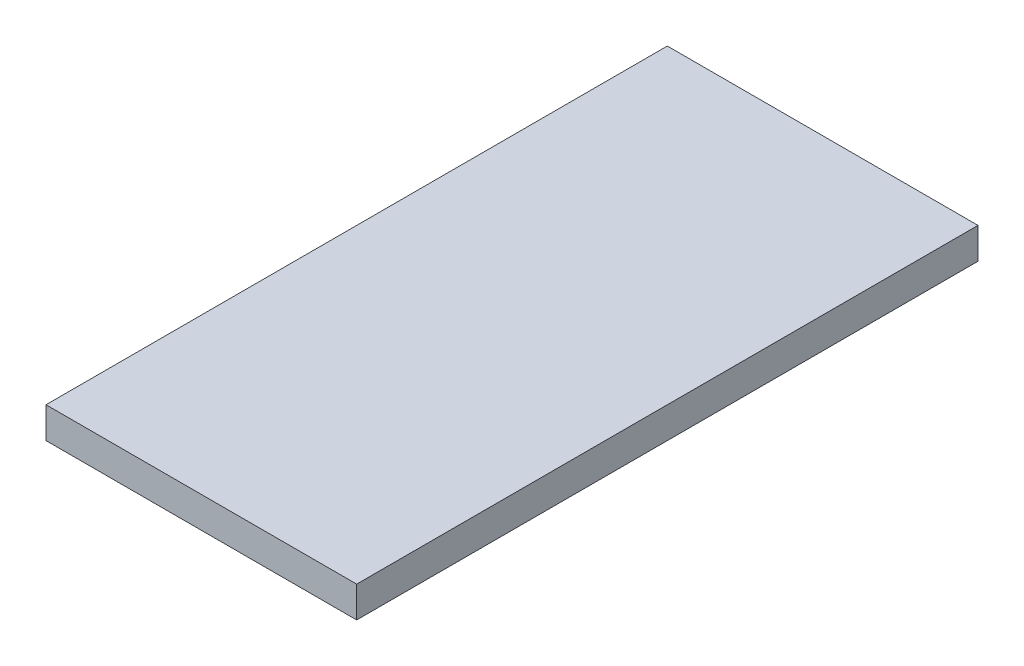
SolidWorks part; units mm, degrees
ref_plane "Front Plane" through (0, 0, 0) normal (0, 0, 1) x (1, 0, 0)
ref_plane "Top Plane" through (0, 0, 0) normal (0, 1, 0) x (1, 0, 0)
ref_plane "Right Plane" through (0, 0, 0) normal (1, 0, 0) x (0, 0, -1)
sketch "Sketch1" plane through (0, 0, 0) normal (0, 1, 0) x (1, 0, 0)
  line L1 (-10, -20) -> (10, -20)
  line L2 (-10, -20) -> (-10, 20)
  line L3 (-10, 20) -> (10, 20)
  line L4 (10, -20) -> (10, 20)
  line L5 (-10, -20) -> (10, 20) construction
  line L6 (-10, 20) -> (10, -20) construction
  point P0 (0, 0)
  dimension "D1" = 20
  dimension "D2" = 40
extrude "Boss-Extrude1" add sketch "Sketch1" along normal blind 2
